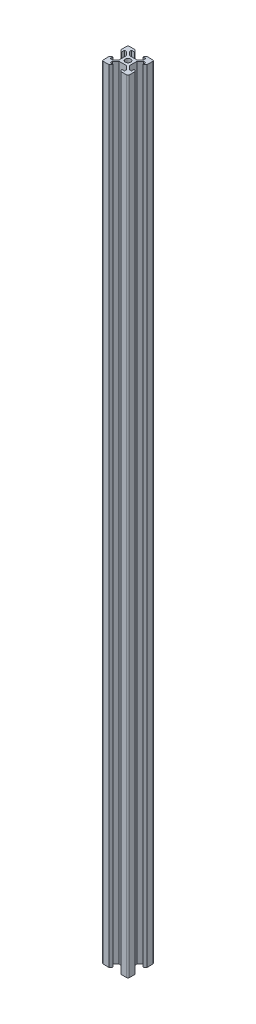
SolidWorks part; units mm, degrees
ref_plane "Front Plane" through (0, 0, 0) normal (0, 0, 1) x (1, 0, 0)
ref_plane "Top Plane" through (0, 0, 0) normal (0, 1, 0) x (1, 0, 0)
ref_plane "Right Plane" through (0, 0, 0) normal (1, 0, 0) x (0, 0, -1)
sketch "Sketch1" plane through (0, 0, 0) normal (0, 1, 0) x (1, 0, 0)
  line L0 (-3.125, 8.2) -> (-4.58, 10)
  line L1 (-9, 10) -> (9, 10)
  line L2 (-10, 9) -> (-10, -9)
  line L3 (-9, -10) -> (9, -10)
  line L4 (10, 9) -> (10, -9)
  line L5 (-10, 10) -> (10, -10) construction
  line L6 (-10, -10) -> (10, 10) construction
  line L7 (-10, 0) -> (0, 0) construction
  line L8 (0, 10) -> (0, 0) construction
  line L9 (-8.2, 3.125) -> (-10, 4.58)
  line L10 (-8.2, 3.125) -> (-8.2, 5.5)
  line L11 (-3.125, 8.2) -> (-5.5, 8.2)
  line L12 (-5.5, 8.2) -> (-5.5, 6.56)
  line L13 (-2.84, 3.9) -> (2.84, 3.9)
  line L14 (-5.5, 6.56) -> (-2.84, 3.9)
  line L15 (-8.2, 5.5) -> (-6.56, 5.5)
  line L16 (-6.56, 5.5) -> (-3.9, 2.84)
  line L17 (-3.9, 2.84) -> (-3.9, -2.84)
  line L18 (3.9, 2.84) -> (3.9, -2.84)
  line L19 (6.56, 5.5) -> (3.9, 2.84)
  line L20 (8.2, 5.5) -> (6.56, 5.5)
  line L21 (8.2, 3.125) -> (8.2, 5.5)
  line L22 (8.2, 3.125) -> (10, 4.58)
  line L23 (3.125, 8.2) -> (4.58, 10)
  line L24 (3.125, 8.2) -> (5.5, 8.2)
  line L25 (5.5, 8.2) -> (5.5, 6.56)
  line L26 (5.5, 6.56) -> (2.84, 3.9)
  line L27 (-8.2, -3.125) -> (-10, -4.58)
  line L28 (-8.2, -3.125) -> (-8.2, -5.5)
  line L29 (-8.2, -5.5) -> (-6.56, -5.5)
  line L30 (-6.56, -5.5) -> (-3.9, -2.84)
  line L31 (8.2, -3.125) -> (10, -4.58)
  line L32 (8.2, -3.125) -> (8.2, -5.5)
  line L33 (8.2, -5.5) -> (6.56, -5.5)
  line L34 (6.56, -5.5) -> (3.9, -2.84)
  line L35 (5.5, -6.56) -> (2.84, -3.9)
  line L36 (5.5, -8.2) -> (5.5, -6.56)
  line L37 (3.125, -8.2) -> (5.5, -8.2)
  line L38 (3.125, -8.2) -> (4.58, -10)
  line L39 (-5.5, -6.56) -> (-2.84, -3.9)
  line L40 (-2.84, -3.9) -> (2.84, -3.9)
  line L41 (-5.5, -8.2) -> (-5.5, -6.56)
  line L42 (-3.125, -8.2) -> (-5.5, -8.2)
  line L43 (-3.125, -8.2) -> (-4.58, -10)
  circle A0 centre (0, 0) radius 2.1
  arc A1 (-10, -9) -> (-9, -10) centre (-9, -9) ccw
  arc A2 (9, -10) -> (10, -9) centre (9, -9) ccw
  arc A3 (9, 10) -> (10, 9) centre (9, 9) cw
  arc A4 (-9, 10) -> (-10, 9) centre (-9, 9) ccw
  point P0 (0, 0)
  point P35 (0, 3.9)
  point P40 (-3.9, 0)
  point P41 (3.9, 0)
  dimension "D3" = 4.2
  dimension "D2" = 1
  dimension "D1" = 20
  dimension "D4" = 6.1
  dimension "D5" = 6.25
  dimension "D6" = 11
  dimension "D7" = 5.68
  dimension "D8" = 9.16
  dimension "D9" = 1.8
extrude "Boss-Extrude1" add sketch "Sketch1" along normal blind 600 contours L43 L42 L41 L39 L40 L35 L36 L37 L38 L3 L4 L31 L32 L33 L34 L18 L19 L20 L21 L22 L1 L23 L24 L25 L26 L13 L14 L12 L11 L0 L2 L9 L10 L15 L16 L17 L30 L29 L28 L27 A0
